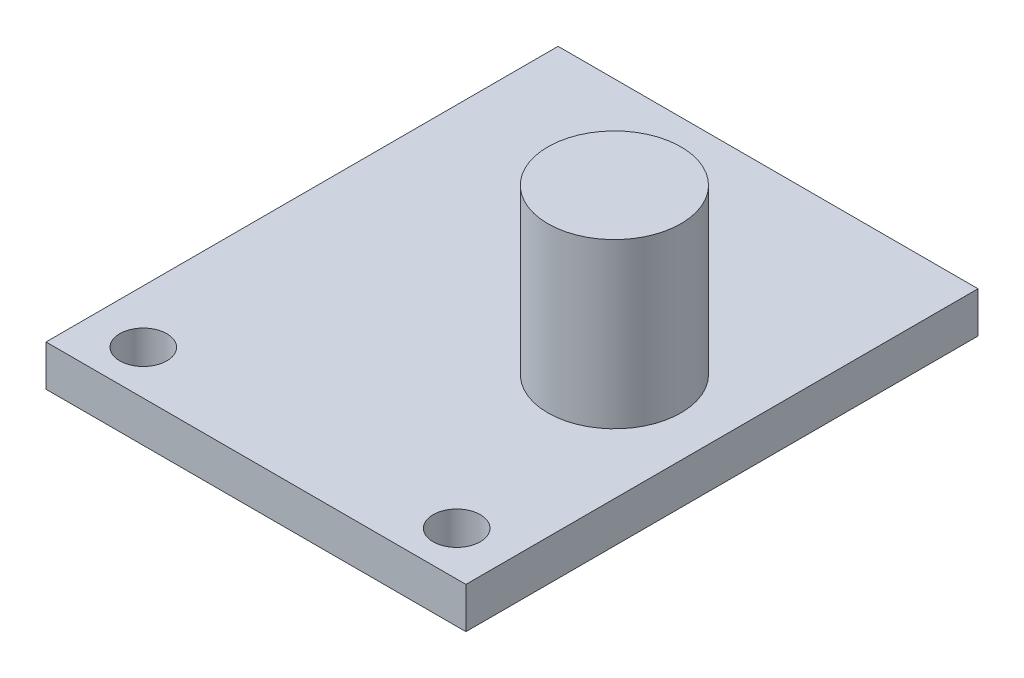
SolidWorks part; units mm, degrees
ref_plane "Front Plane" through (0, 0, 0) normal (0, 0, 1) x (1, 0, 0)
ref_plane "Top Plane" through (0, 0, 0) normal (0, 1, 0) x (1, 0, 0)
ref_plane "Right Plane" through (0, 0, 0) normal (1, 0, 0) x (0, 0, -1)
sketch "Sketch1" plane through (0, 0, 0) normal (0, 1, 0) x (1, 0, 0)
  line L1 (-10.25, -12.5) -> (10.25, -12.5)
  line L2 (-10.25, -12.5) -> (-10.25, 12.5)
  line L3 (-10.25, 12.5) -> (10.25, 12.5)
  line L4 (10.25, -12.5) -> (10.25, 12.5)
  line L5 (-10.25, -12.5) -> (10.25, 12.5) construction
  line L6 (-10.25, 12.5) -> (10.25, -12.5) construction
  point P0 (0, 0)
  dimension "D1" = 20.5
  dimension "D2" = 25
extrude "Boss-Extrude1" add sketch "Sketch1" along normal blind 2
sketch "Sketch2" plane through (0, 2, 0) normal (0, 1, 0) x (1, 0, 0)
  line L0 (-6.5, -10.35) -> (6.5, -10.35) construction
  line L1 (-7.65, -11.5) -> (-7.65, -12.5) construction
  line L2 (-10.25, -12.5) -> (10.25, -12.5) construction
  circle A0 centre (7.65, -10.35) radius 1.15
  circle A2 centre (-7.65, -10.35) radius 1.15
  point P6 (0, -10.35)
  dimension "D1" = 2.3
  dimension "D2" = 2.3
  dimension "D3" = 13
  dimension "D4" = 1
extrude "Cut-Extrude1" cut sketch "Sketch2" against normal through all
sketch "Sketch3" plane through (0, 2, 0) normal (0, 1, 0) x (1, 0, 0)
  circle A0 centre (5, 0) radius 3.25
  dimension "D1" = 6.5
  dimension "D2" = 5
extrude "Boss-Extrude2" add sketch "Sketch3" along normal blind 8
